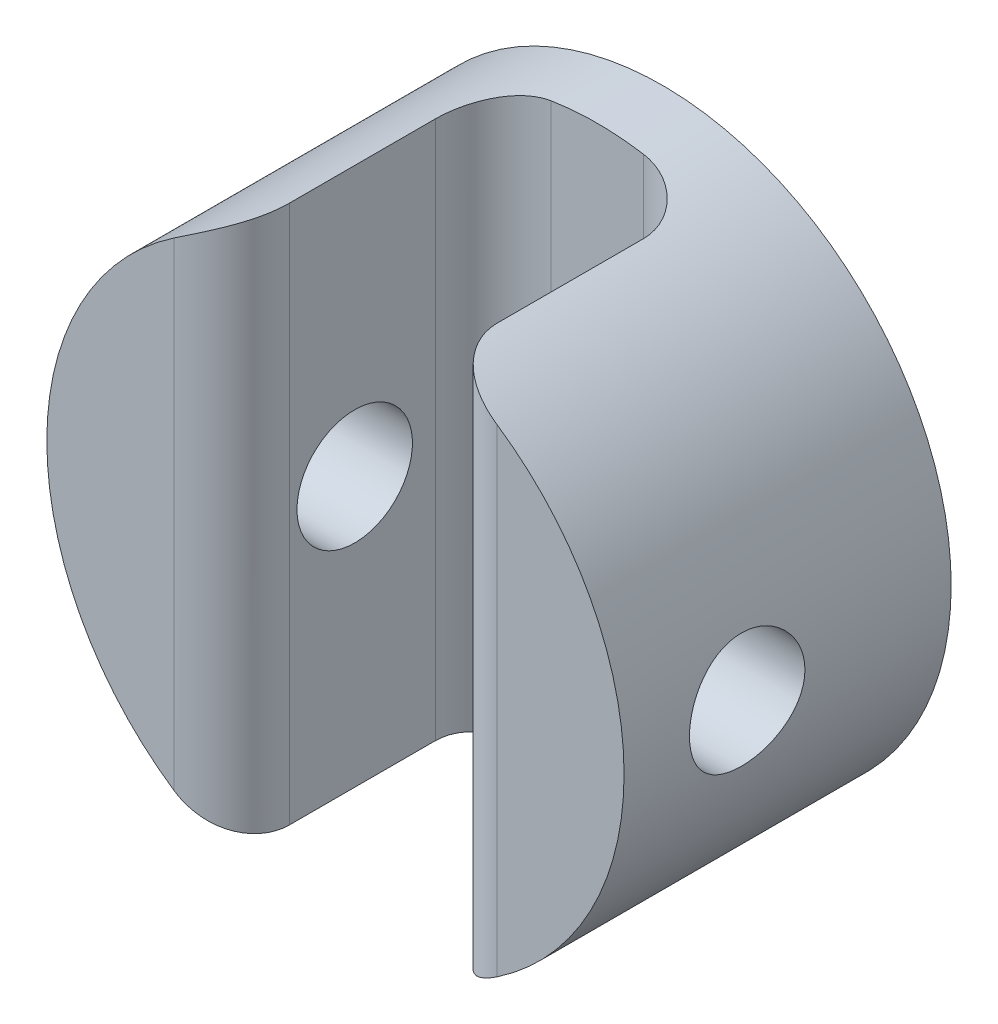
SolidWorks part; units mm, degrees
ref_plane "Front Plane" through (0, 0, 0) normal (0, 0, 1) x (1, 0, 0)
ref_plane "Top Plane" through (0, 0, 0) normal (0, 1, 0) x (1, 0, 0)
ref_plane "Right Plane" through (0, 0, 0) normal (1, 0, 0) x (0, 0, -1)
sketch "Sketch1" plane through (0, 0, 0) normal (0, 0, 1) x (1, 0, 0)
  circle A0 centre (0, 0) radius 7.5
  dimension "D1" = 15
extrude "Boss-Extrude1" add sketch "Sketch1" along normal blind 8.5
sketch "Sketch2" plane through (0, 0, 8.5) normal (0, 0, 1) x (1, 0, 0)
  line L0 (0, 0) -> (2.7, 0) construction
  line L1 (0, 0) -> (-2.7, 0) construction
  line L2 (2.7, 0) -> (2.7, 13.7828)
  line L3 (-2.7, 0) -> (-2.7, 13.7828)
  line L4 (-2.7, 13.7828) -> (2.7, 13.7828)
  line L5 (2.7, 0) -> (2.7, -14.1285)
  line L6 (2.7, -14.1285) -> (-2.7, -14.1285)
  line L7 (-2.7, -14.1285) -> (-2.7, 0)
  dimension "D1" = 2.7
  dimension "D2" = 2.7
extrude "Cut-Extrude1" cut sketch "Sketch2" against normal blind 6.8
sketch "Sketch3" plane through (-2.7, 0, 0) normal (1, 0, 0) x (0, 0, -1)
  line L0 (-8.5, 0) -> (-5.3, 0) construction
  line L1 (-8.5, 6.9971) -> (-8.5, -6.9971) construction
  circle A0 centre (-5.3, 0) radius 1.5
  dimension "D1" = 3.2
extrude "Cut-Extrude2" cut sketch "Sketch3" along normal through all and the other way through all
fillet "Fillet1" radius 1.5 4 edges at (2.7, 0, 8.5) (2.7, 0, 1.7) (-2.7, 0, 1.7) (-2.7, 0, 8.5)
